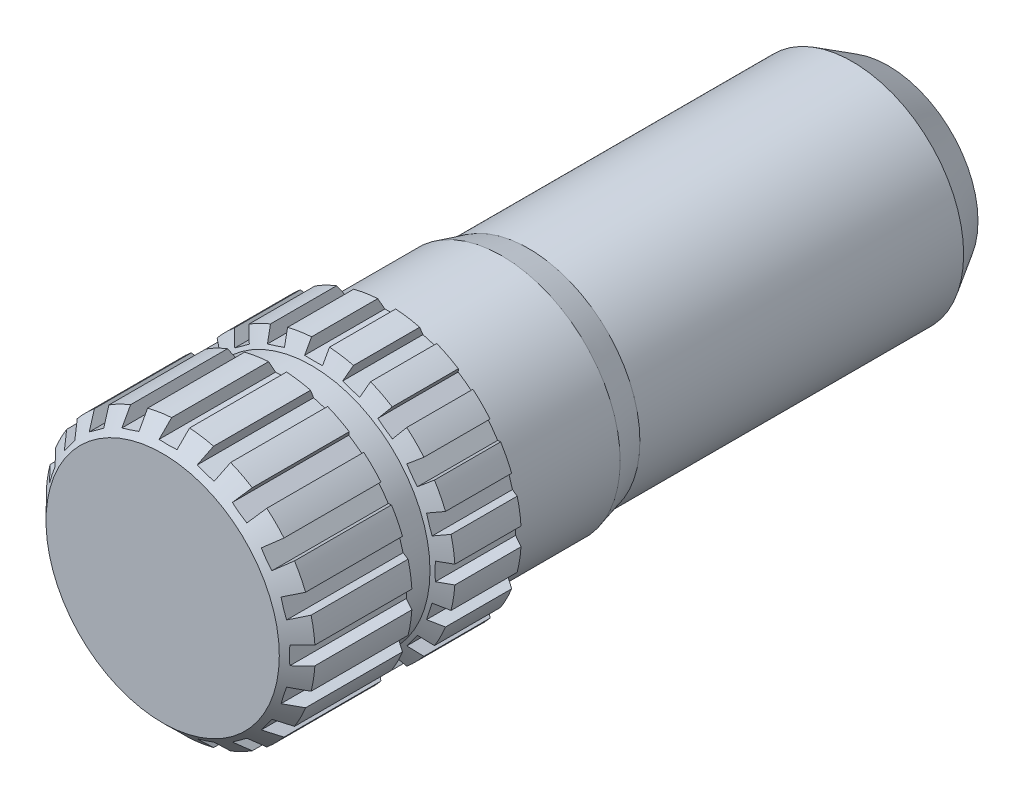
SolidWorks part; units mm, degrees
material "Plain Carbon Steel"
ref_plane "Front Plane" through (0, 0, 0) normal (0, 0, 1) x (1, 0, 0)
ref_plane "Top Plane" through (0, 0, 0) normal (0, 1, 0) x (1, 0, 0)
ref_plane "Right Plane" through (0, 0, 0) normal (1, 0, 0) x (0, 0, -1)
sketch "Sketch1" plane through (0, 0, 0) normal (1, 0, 0) x (0, 0, -1)
  line L0 (-33.568, 0) -> (-33.568, 9.525)
  line L1 (0.2915, 0) -> (-49999.7085, 0) construction
  line L2 (-33.568, 9.525) -> (-25.4363, 9.525)
  line L3 (-25.4363, 9.525) -> (-24.8013, 8.382)
  line L4 (-24.8013, 8.382) -> (-23.0306, 8.382)
  line L5 (-23.0306, 8.382) -> (-22.3956, 9.525)
  line L6 (-22.3956, 9.525) -> (-17.7133, 9.525)
  line L7 (-17.7133, 9.525) -> (-17.058, 8.382)
  line L8 (-17.058, 8.382) -> (-9.5738, 8.382)
  line L9 (-9.5738, 8.382) -> (-7.6688, 7.874)
  line L10 (-7.6688, 7.874) -> (15.24, 7.874)
  line L11 (15.24, 7.874) -> (17.78, 6.35)
  line L12 (17.78, 6.35) -> (17.78, 0)
  line L13 (-23.916, 8.382) -> (-23.916, 6.8449) construction
  line L14 (-33.568, 0) -> (17.78, 0)
  dimension "D1" = 9.525
  dimension "D2" = 7.874
  dimension "D3" = 8.382
  dimension "D4" = 1.905
  dimension "D5" = 17.78
  dimension "D6" = 6.35
  dimension "D7" = 22.9088
  dimension "D8" = 2.54
  dimension "D9" = 0.635
  dimension "D10" = 33.568
  dimension "D11" = 1.7706
  dimension "D12" = 0.635
  dimension "D13" = 0.6553
  dimension "D14" = 9.652
  dimension "D15" = 16.51
revolve "Revolve1" add sketch "Sketch1" angle 360 about L1
sketch "Sketch2" plane through (0, 0, 33.568) normal (0, 0, 1) x (1, 0, 0)
  line L0 (0, 0) -> (0, 10.0398) construction
  line L1 (-0.635, 8.6148) -> (0.635, 8.6148)
  line L2 (0.635, 8.6148) -> (0.635, 9.5038)
  line L3 (-0.635, 8.6148) -> (-0.635, 9.5038)
  line L4 (2.0582, 8.3894) -> (2.3329, 9.2349)
  line L5 (2.0582, 8.3894) -> (3.266, 7.9969)
  line L6 (3.266, 7.9969) -> (3.5408, 8.8424)
  line L7 (4.5499, 7.3428) -> (5.0725, 8.062)
  line L8 (4.5499, 7.3428) -> (5.5774, 6.5963)
  line L9 (5.5774, 6.5963) -> (6.0999, 7.3155)
  line L10 (6.5963, 5.5774) -> (7.3155, 6.0999)
  line L11 (6.5963, 5.5774) -> (7.3428, 4.5499)
  line L12 (7.3428, 4.5499) -> (8.062, 5.0725)
  line L13 (7.9969, 3.266) -> (8.8424, 3.5408)
  line L14 (7.9969, 3.266) -> (8.3894, 2.0582)
  line L15 (8.3894, 2.0582) -> (9.2349, 2.3329)
  line L16 (8.6148, 0.635) -> (9.5038, 0.635)
  line L17 (8.6148, 0.635) -> (8.6148, -0.635)
  line L18 (8.6148, -0.635) -> (9.5038, -0.635)
  line L19 (8.3894, -2.0582) -> (9.2349, -2.3329)
  line L20 (8.3894, -2.0582) -> (7.9969, -3.266)
  line L21 (7.9969, -3.266) -> (8.8424, -3.5408)
  line L22 (7.3428, -4.5499) -> (8.062, -5.0725)
  line L23 (7.3428, -4.5499) -> (6.5963, -5.5774)
  line L24 (6.5963, -5.5774) -> (7.3155, -6.0999)
  line L25 (5.5774, -6.5963) -> (6.0999, -7.3155)
  line L26 (5.5774, -6.5963) -> (4.5499, -7.3428)
  line L27 (4.5499, -7.3428) -> (5.0725, -8.062)
  line L28 (3.266, -7.9969) -> (3.5408, -8.8424)
  line L29 (3.266, -7.9969) -> (2.0582, -8.3894)
  line L30 (2.0582, -8.3894) -> (2.3329, -9.2349)
  line L31 (0.635, -8.6148) -> (0.635, -9.5038)
  line L32 (0.635, -8.6148) -> (-0.635, -8.6148)
  line L33 (-0.635, -8.6148) -> (-0.635, -9.5038)
  line L34 (-2.0582, -8.3894) -> (-2.3329, -9.2349)
  line L35 (-2.0582, -8.3894) -> (-3.266, -7.9969)
  line L36 (-3.266, -7.9969) -> (-3.5408, -8.8424)
  line L37 (-4.5499, -7.3428) -> (-5.0725, -8.062)
  line L38 (-4.5499, -7.3428) -> (-5.5774, -6.5963)
  line L39 (-5.5774, -6.5963) -> (-6.0999, -7.3155)
  line L40 (-6.5963, -5.5774) -> (-7.3155, -6.0999)
  line L41 (-6.5963, -5.5774) -> (-7.3428, -4.5499)
  line L42 (-7.3428, -4.5499) -> (-8.062, -5.0725)
  line L43 (-7.9969, -3.266) -> (-8.8424, -3.5408)
  line L44 (-7.9969, -3.266) -> (-8.3894, -2.0582)
  line L45 (-8.3894, -2.0582) -> (-9.2349, -2.3329)
  line L46 (-8.6148, -0.635) -> (-9.5038, -0.635)
  line L47 (-8.6148, -0.635) -> (-8.6148, 0.635)
  line L48 (-8.6148, 0.635) -> (-9.5038, 0.635)
  line L49 (-8.3894, 2.0582) -> (-9.2349, 2.3329)
  line L50 (-8.3894, 2.0582) -> (-7.9969, 3.266)
  line L51 (-7.9969, 3.266) -> (-8.8424, 3.5408)
  line L52 (-7.3428, 4.5499) -> (-8.062, 5.0725)
  line L53 (-7.3428, 4.5499) -> (-6.5963, 5.5774)
  line L54 (-6.5963, 5.5774) -> (-7.3155, 6.0999)
  line L55 (-5.5774, 6.5963) -> (-6.0999, 7.3155)
  line L56 (-5.5774, 6.5963) -> (-4.5499, 7.3428)
  line L57 (-4.5499, 7.3428) -> (-5.0725, 8.062)
  line L58 (-3.266, 7.9969) -> (-3.5408, 8.8424)
  line L59 (-3.266, 7.9969) -> (-2.0582, 8.3894)
  line L60 (-2.0582, 8.3894) -> (-2.3329, 9.2349)
  circle A0 centre (0, 0) radius 9.525 construction
  arc A1 (-8.062, 5.0725) -> (-8.8424, 3.5408) centre (0, 0) ccw
  arc A2 (-6.0999, 7.3155) -> (-7.3155, 6.0999) centre (0, 0) ccw
  arc A3 (-3.5408, 8.8424) -> (-5.0725, 8.062) centre (0, 0) ccw
  arc A4 (-0.635, 9.5038) -> (-2.3329, 9.2349) centre (0, 0) ccw
  arc A5 (2.3329, 9.2349) -> (0.635, 9.5038) centre (0, 0) ccw
  arc A6 (5.0725, 8.062) -> (3.5408, 8.8424) centre (0, 0) ccw
  arc A7 (7.3155, 6.0999) -> (6.0999, 7.3155) centre (0, 0) ccw
  arc A8 (8.8424, 3.5408) -> (8.062, 5.0725) centre (0, 0) ccw
  arc A9 (9.5038, 0.635) -> (9.2349, 2.3329) centre (0, 0) ccw
  arc A10 (9.2349, -2.3329) -> (9.5038, -0.635) centre (0, 0) ccw
  arc A11 (8.062, -5.0725) -> (8.8424, -3.5408) centre (0, 0) ccw
  arc A12 (6.0999, -7.3155) -> (7.3155, -6.0999) centre (0, 0) ccw
  arc A13 (3.5408, -8.8424) -> (5.0725, -8.062) centre (0, 0) ccw
  arc A14 (0.635, -9.5038) -> (2.3329, -9.2349) centre (0, 0) ccw
  arc A15 (-2.3329, -9.2349) -> (-0.635, -9.5038) centre (0, 0) ccw
  arc A16 (-5.0725, -8.062) -> (-3.5408, -8.8424) centre (0, 0) ccw
  arc A17 (-7.3155, -6.0999) -> (-6.0999, -7.3155) centre (0, 0) ccw
  arc A18 (-8.8424, -3.5408) -> (-8.062, -5.0725) centre (0, 0) ccw
  arc A19 (-9.5038, -0.635) -> (-9.2349, -2.3329) centre (0, 0) ccw
  arc A20 (-9.2349, 2.3329) -> (-9.5038, 0.635) centre (0, 0) ccw
  point P10 (0, 8.6148)
  dimension "D1" = 0.635
  dimension "D2" = 0.889
  dimension "D3" = 20
chamfer "Chamfer1" distance 1.27 angle 45 1 edges at (-9.525, 0, 33.568)
extrude "Cut-Extrude1" cut sketch "Sketch2" against normal through all flip side to cut
